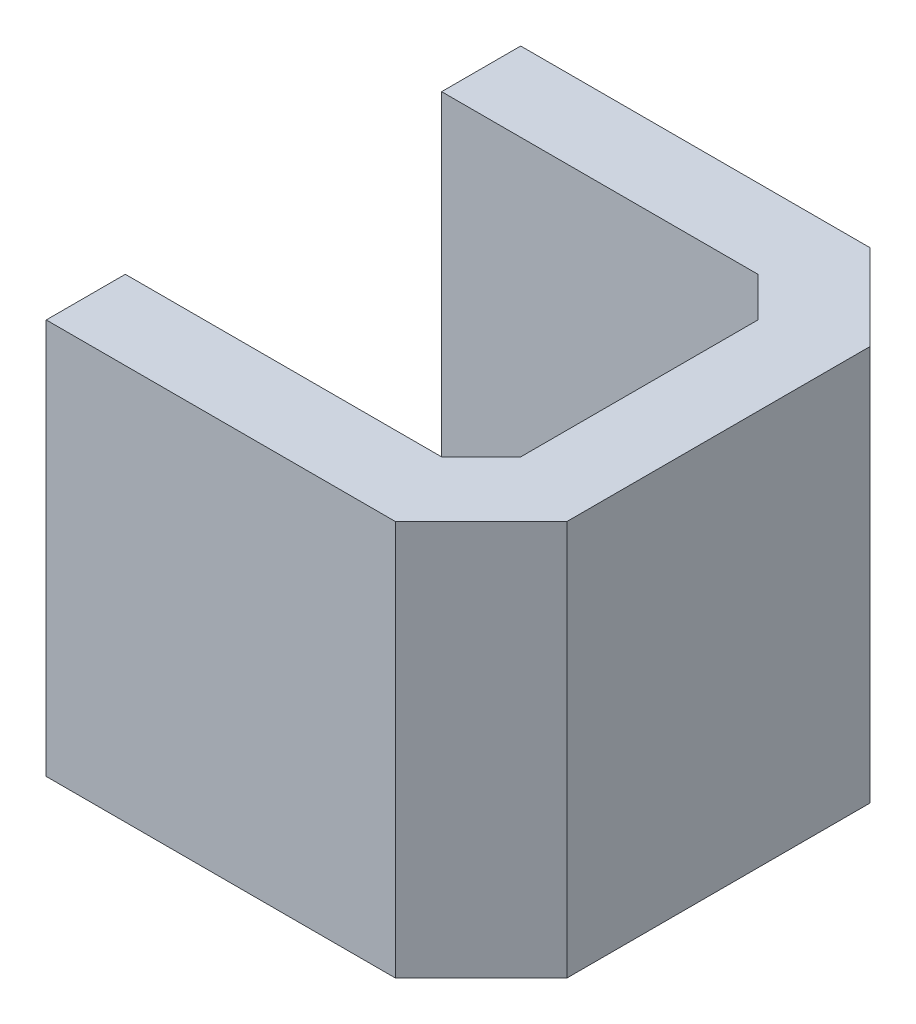
SolidWorks part; units mm, degrees
ref_plane "Front Plane" through (0, 0, 0) normal (0, 0, 1) x (1, 0, 0)
ref_plane "Top Plane" through (0, 0, 0) normal (0, 1, 0) x (1, 0, 0)
ref_plane "Right Plane" through (0, 0, 0) normal (1, 0, 0) x (0, 0, -1)
sketch "Sketch1" plane through (0, 0, 0) normal (0, 1, 0) x (1, 0, 0)
  line L0 (-3, 0) -> (6, 0) construction
  line L1 (-4, 4) -> (4, 4)
  line L3 (-4, -4) -> (4, -4)
  line L4 (4, 4) -> (4, -4) construction
  line L5 (-4, 4) -> (4, -4) construction
  line L6 (-4, -4) -> (4, 4) construction
  line L7 (4, 4) -> (5, 3)
  line L8 (5, -3) -> (4, -4)
  line L9 (5, 3) -> (5, -3)
  line L10 (-4, 6) -> (4.8284, 6)
  line L11 (4.8284, 6) -> (7, 3.8284)
  line L12 (7, 3.8284) -> (7, -3.8284)
  line L13 (7, -3.8284) -> (4.8284, -6)
  line L14 (-4, -6) -> (4.8284, -6)
  line L15 (-4, 4) -> (-4, 6)
  line L16 (-4, -4) -> (-4, -6)
  point P0 (0, 0)
  point P8 (4, 0)
  dimension "D1" = 8
  dimension "D2" = 8
  dimension "D3" = 2
  dimension "D4" = 4
  dimension "D5" = 6
  dimension "D6" = 3
  dimension "D7" = 2
extrude "Boss-Extrude1" add sketch "Sketch1" along normal blind 10
